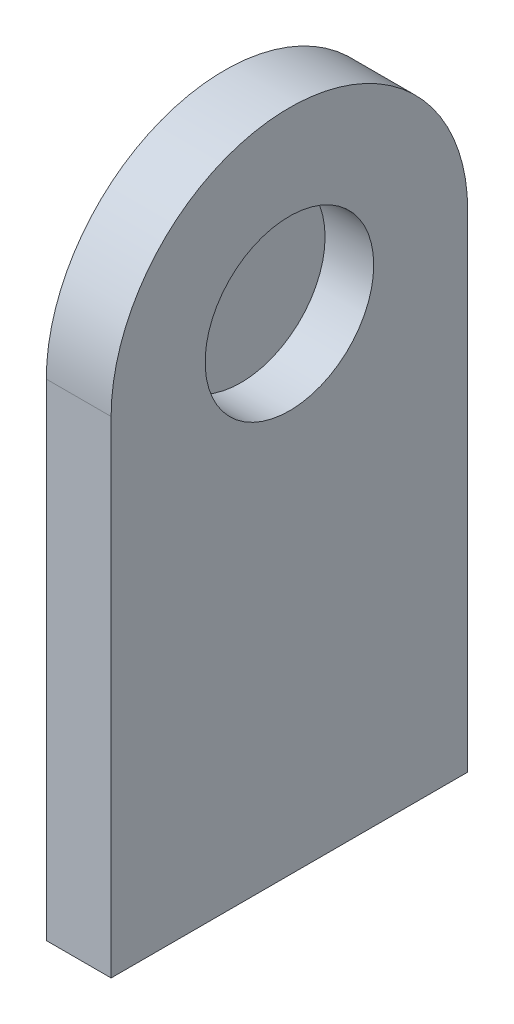
SolidWorks part; units mm, degrees
ref_plane "Front Plane" through (0, 0, 0) normal (0, 0, 1) x (1, 0, 0)
ref_plane "Top Plane" through (0, 0, 0) normal (0, 1, 0) x (1, 0, 0)
ref_plane "Right Plane" through (0, 0, 0) normal (1, 0, 0) x (0, 0, -1)
sketch "Sketch2" plane through (0, 0, 0) normal (1, 0, 0) x (0, 0, -1)
  line L1 (55, 75) -> (-55, 75)
  line L2 (55, 75) -> (55, -75)
  line L3 (55, -75) -> (-55, -75)
  line L4 (-55, 75) -> (-55, -75)
  line L5 (55, 75) -> (-55, -75) construction
  line L6 (55, -75) -> (-55, 75) construction
  circle A0 centre (0, 75) radius 55
  point P0 (0, 0)
  dimension "D1" = 110
  dimension "D2" = 150
extrude "Boss-Extrude1" add sketch "Sketch2" along normal blind 20 contours A0 L4 L3 L2 | L1 A0 | L1 A0
sketch "Sketch3" plane through (20, 0, 0) normal (1, 0, 0) x (0, 0, -1)
  circle A0 centre (0, 75) radius 26
  dimension "D1" = 52
extrude "Cut-Extrude1" cut sketch "Sketch3" against normal blind 15
sketch "Sketch5" plane through (0, -75, 0) normal (0, -1, 0) x (1, 0, 0)
  line L0 (10, 55) -> (10, -55) construction
  line L1 (20, 55) -> (0, 55) construction
  line L2 (20, -55) -> (0, -55) construction
  point P6 (10, 36.6667)
  point P7 (10, 18.3333)
  point P8 (10, 0)
  point P9 (10, -18.3333)
  point P10 (10, -36.6667)
hole_wizard "Tap Drill for M6x1.0 Tap2" positions "Sketch9" profile "Sketch10" hole size "M6x1.0" standard "ANSI Metric"
sketch "Sketch9" plane through (0, -75, 0) normal (0, -1, 0) x (-1, 0, 0)
  line L0 (-10, -55) -> (-10, 55) construction
  point P0 (-10, -36.6667)
  point P3 (-10, -18.3333)
  point P6 (-10, 0)
  point P10 (-10, 18.3333)
  point P13 (-10, 36.6667)
sketch "Sketch10" plane through (10, -75, 36.6667) normal (1, 0, 0) x (0, 0, -1)
  line L0 (0, 0) -> (0, 41.5022)
  line L1 (0, 41.5022) -> (2.5, 40)
  line L2 (2.5, 40) -> (2.5, 0)
  line L5 (2.5, 0) -> (0, 0)
  line L10 (0, 41.5022) -> (-2.5, 40) construction
  line L11 (0, -6.35) -> (0, 107.95) construction
  dimension "Hole Dia." = 5
  dimension "Hole Depth" = 40
  dimension "Drill Angle" = 118
equation "\"GearDiameter\"= 80mm"
equation "\"WormGearDiam\"= 40mm"
equation "\"WormAngle\"= 20"
equation "\"WormLength\"= 40mm"
equation "\"WormHubDiam\"= 25mm"
